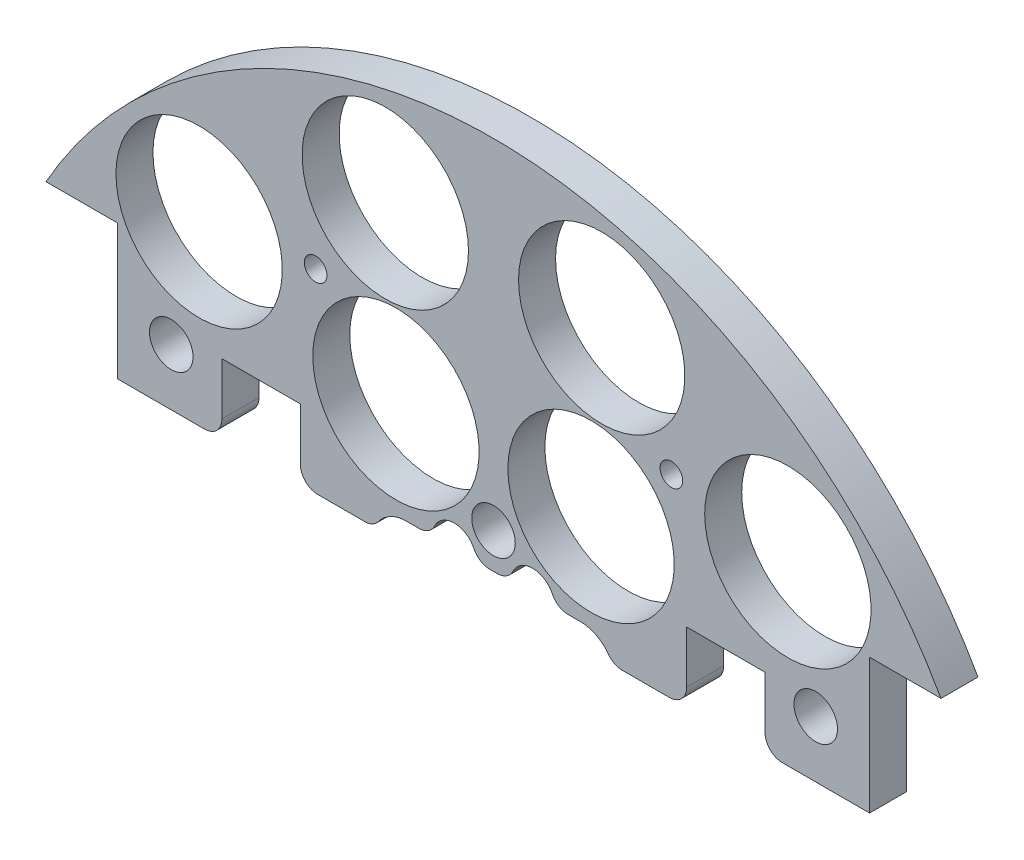
SolidWorks part; units mm, degrees
ref_plane "Front Plane" through (0, 0, 0) normal (0, 0, 1) x (1, 0, 0)
ref_plane "Top Plane" through (0, 0, 0) normal (0, 1, 0) x (1, 0, 0)
ref_plane "Right Plane" through (0, 0, 0) normal (1, 0, 0) x (0, 0, -1)
sketch "Sketch1" plane through (0, 0, 0) normal (0, 0, 1) x (1, 0, 0)
  line L0 (0, 0) -> (-82.1241, 0) construction
  line L1 (0, 0) -> (0, 95.6219) construction
  line L3 (-65.2538, 36.83) -> (-54.8398, 36.83)
  line L5 (-65.2538, -36.83) -> (-54.8398, -36.83)
  line L6 (-54.8398, 36.83) -> (-54.8398, -36.83)
  line L7 (65.2538, -36.83) -> (54.8398, -36.83)
  line L8 (65.2538, 36.83) -> (54.8398, 36.83)
  line L9 (54.8398, 36.83) -> (54.8398, -36.83)
  arc A0 (-65.2538, -36.83) -> (65.2538, -36.83) centre (0, 0) ccw
  circle A1 centre (-45.466, 11.049) radius 1.651
  circle A2 centre (-20.0673, 10.795) radius 1.651
  circle A3 centre (-20.0673, -10.795) radius 1.651
  circle A4 centre (-45.466, -11.049) radius 1.651
  circle A5 centre (45.466, -11.049) radius 1.651
  circle A6 centre (20.0673, -10.795) radius 1.651
  circle A7 centre (20.0673, 10.795) radius 1.651
  circle A8 centre (45.466, 11.049) radius 1.651
  arc A9 (65.2538, 36.83) -> (-65.2538, 36.83) centre (0, 0) ccw
  dimension "D2" = 3.302
  dimension "D3" = 3.302
  dimension "D4" = 25.4
  dimension "D5" = 10.795
  dimension "D10" = 45.466
  dimension "D6" = 73.66
  dimension "D7" = 10.414
  dimension "D8" = 74.93
  dimension "D9" = 74.93
  dimension "D11" = 36.83
extrude "Boss-Extrude2" add sketch "Sketch1" along normal blind 5.3975
sketch "Sketch2" plane through (0, 0, 5.3975) normal (0, 0, 1) x (1, 0, 0)
  line L0 (0, 68.58) -> (0, 55.88) construction
  line L1 (-9.525, 68.58) -> (9.525, 68.58)
  line L2 (-9.525, 68.58) -> (-9.525, 55.88)
  line L3 (-9.525, 55.88) -> (9.525, 55.88)
  line L4 (9.525, 68.58) -> (9.525, 55.88)
  line L5 (-9.525, 62.23) -> (9.525, 62.23) construction
  arc A0 (65.2538, 36.83) -> (-65.2538, 36.83) centre (0, 0) ccw construction
  circle A1 centre (-20.0673, 10.795) radius 1.651 construction
  circle A2 centre (20.0673, 10.795) radius 1.651 construction
  circle A3 centre (-6.731, 62.23) radius 1.143
  circle A4 centre (6.731, 62.23) radius 1.143
  dimension "D4" = 2.286
  dimension "D5" = 0
  dimension "D6" = 6.731
  dimension "D1" = 19.05
  dimension "D2" = 12.7
  dimension "D3" = 55.88
extrude "Cut-Extrude1" cut sketch "Sketch2" against normal through all contours A3 | A4
sketch "Sketch3" plane through (0, 0, 0) normal (0, 0, -1) x (-1, 0, 0)
  line L0 (0, 0) -> (0, -116.2908) construction
  line L1 (0, 0) -> (-153.8039, 0) construction
  circle A0 centre (-14.224, -56.7251) radius 12.1285
  circle A3 centre (14.224, -56.7251) radius 12.1285
  circle A4 centre (-42.926, -42.926) radius 12.1285
  circle A5 centre (14.224, 34.29) radius 12.1285
  circle A6 centre (-14.224, 34.29) radius 12.1285
  circle A8 centre (-42.926, 42.926) radius 12.1285
  circle A11 centre (42.926, 42.926) radius 12.1285
  circle A14 centre (42.926, -42.926) radius 12.1285
  point P36 (0, 0)
  point P53 (0, 0)
  point P55 (0, 0)
  dimension "D1" = 34.29
  dimension "D2" = 14.224
  dimension "D3" = 24.257
  dimension "D4" = 42.926
  dimension "D5" = 42.926
extrude "Cut-Extrude2" cut sketch "Sketch3" against normal through all
sketch "Sketch4" plane through (0, 0, 0) normal (0, 0, -1) x (-1, 0, 0)
  line L1 (-15.7702, 56.3138) -> (12.7925, 56.3138)
  line L2 (-15.7702, 56.3138) -> (-15.7702, 67.9913)
  line L3 (-15.7702, 67.9913) -> (12.7925, 67.9913)
  line L4 (12.7925, 56.3138) -> (12.7925, 67.9913)
extrude "Boss-Extrude3" add sketch "Sketch4" against normal up to surface (5.3975 mm away) up to face at (-55.0545, -42.926, 5.3975)
sketch "Sketch5" plane through (0, 0, 0) normal (0, 0, -1) x (-1, 0, 0)
  line L1 (-113.3786, -90.442) -> (117.3207, -90.442)
  line L2 (-113.3786, -90.442) -> (-113.3786, 17.145)
  line L3 (-113.3786, 17.145) -> (117.3207, 17.145)
  line L4 (117.3207, -90.442) -> (117.3207, 17.145)
  circle A1 centre (20.0673, 10.795) radius 1.651 construction
  dimension "D1" = 6.35
extrude "Cut-Extrude3" cut sketch "Sketch5" against normal through all
sketch "Sketch6" plane through (0, 0, 0) normal (0, 0, -1) x (-1, 0, 0)
  line L0 (0, 0) -> (0, 74.93) construction
  line L1 (0, 0) -> (-15.5068, 57.8721) construction
  arc A0 (65.2538, 36.83) -> (-65.2538, 36.83) centre (0, 0) ccw construction
  circle A1 centre (-15.7776, 58.8828) radius 12.1285
  circle A3 centre (15.7776, 58.8828) radius 12.1285
  dimension "D1" = 24.257
  dimension "D2" = 0
  dimension "D4" = 60.96
  dimension "D3" = 15
extrude "Cut-Extrude4" cut sketch "Sketch6" against normal through all
extrude "Cut-Extrude55" cut sketch "Sketch57" against normal through all both and the other way through all
sketch "Sketch57" plane through (-29.8755, 133.1307, 31.75) normal (0, 0, 1) x (0.01, 0.9999, 0)
  line L0 (-132.559, -31.3134) -> (-132.559, 57.8454) construction
  line L1 (-132.559, -31.3134) -> (-222.516, -31.3134) construction
  circle A0 centre (-157.959, 14.4066) radius 3.175
  circle A1 centre (-173.199, -31.3134) radius 3.175
  circle A3 centre (-157.959, -77.0334) radius 3.175
  circle A4 centre (-107.159, -77.0334) radius 3.175
  circle A5 centre (-91.919, -31.3134) radius 3.175
  circle A6 centre (-107.159, 14.4066) radius 3.175
sketch "Sketch58" [suppressed] plane through (0, 0, 0) normal (0, 0, -1) x (-1, 0, 0)
  circle A0 centre (-46.0825, 25.2068) radius 4.445
  circle A1 centre (-0.5172, 40.9032) radius 4.445
  circle A2 centre (45.3529, 26.1212) radius 4.445
  circle A3 centre (-46.0825, 25.2068) radius 3.175 construction
  circle A4 centre (-0.5172, 40.9032) radius 3.175 construction
  circle A5 centre (45.3529, 26.1212) radius 3.175 construction
  dimension "D1" = 1.27
  dimension "D2" = 1.27
  dimension "D3" = 1.27
extrude "Boss-Extrude4" [suppressed] add sketch "Sketch58" against normal up to surface (6.35 mm away)
extrude "Cut-Extrude56" cut sketch "Sketch59" against normal through all both and the other way through all
sketch "Sketch59" plane through (31.3134, 132.614, -19.05) normal (0, 0, -1) x (0, 1, 0)
  line L0 (-132.614, -31.3134) -> (-132.614, 57.8454) construction
  line L1 (-132.614, -31.3134) -> (-222.516, -31.3134) construction
  circle A0 centre (-158.014, 14.4066) radius 3.175
  circle A1 centre (-173.254, -31.3134) radius 3.175
  circle A3 centre (-158.014, -77.0334) radius 3.175
  circle A4 centre (-107.214, -77.0334) radius 3.175
  circle A5 centre (-91.974, -31.3134) radius 3.175
  circle A6 centre (-107.214, 14.4066) radius 3.175
extrude "Cut-Extrude60" cut sketch "Sketch63" against normal blind 29.21
sketch "Sketch63" plane through (31.3134, 132.614, -15.875) normal (0, 0, -1) x (0, 1, 0)
  line L0 (-132.559, -31.3134) -> (6.1626, -31.3134) construction
  line L2 (-132.559, -31.3134) -> (-132.559, -122.6589) construction
  circle A0 centre (-190.979, 2.9766) radius 1.651
  circle A2 centre (-154.784, -31.3134) radius 1.651
  circle A3 centre (-190.979, -65.6034) radius 1.651
  circle A4 centre (-110.334, -31.3134) radius 1.651
  circle A5 centre (-74.139, -65.6034) radius 1.651
  circle A6 centre (-74.139, 2.9766) radius 1.651
extrude "Cut-Extrude158" cut sketch "Sketch161" against normal blind 29.21
sketch "Sketch161" plane through (-31.3134, 132.559, 6.35) normal (0, 0, 1) x (0, 1, 0)
  line L0 (-143.7712, -34.3645) -> (6.1626, -34.3645) construction
  line L2 (-143.7712, -34.3645) -> (-143.7712, -122.6589) construction
  circle A0 centre (-202.1912, -0.0745) radius 1.651
  circle A2 centre (-165.9962, -34.3645) radius 1.651
  circle A3 centre (-202.1912, -68.6545) radius 1.651
  circle A4 centre (-121.5462, -34.3645) radius 1.651
  circle A5 centre (-85.3512, -68.6545) radius 1.651
  circle A6 centre (-85.3512, -0.0745) radius 1.651
sketch "Sketch162" plane through (0, 0, 5.3975) normal (0, 0, 1) x (1, 0, 0)
  line L0 (-54.8398, 17.145) -> (54.8398, 17.145) construction
  line L1 (39.5998, 17.145) -> (28.1698, 17.145)
  line L2 (39.5998, 17.145) -> (39.5998, 27.305)
  line L3 (39.5998, 27.305) -> (28.1698, 27.305)
  line L4 (28.1698, 17.145) -> (28.1698, 27.305)
  line L5 (0, -4.3124) -> (0, 89.5869) construction
  line L6 (-28.1698, 17.145) -> (-39.5998, 17.145)
  line L7 (-28.1698, 17.145) -> (-28.1698, 27.305)
  line L8 (-28.1698, 27.305) -> (-39.5998, 27.305)
  line L9 (-39.5998, 17.145) -> (-39.5998, 27.305)
  line L10 (54.8398, 17.145) -> (54.8398, 36.83) construction
  dimension "D1" = 10.16
  dimension "D2" = 11.43
  dimension "D3" = 15.24
extrude "Cut-Extrude159" cut sketch "Sketch162" against normal through all
sketch "Sketch202" plane through (0, 0, 0) normal (0, 0, -1) x (-1, 0, 0)
  line L0 (0, 0) -> (0, 91.2173) construction
  circle A0 centre (25.9376, 45.466) radius 1.651
  circle A1 centre (42.926, 42.926) radius 12.1285 construction
  circle A2 centre (15.7776, 58.8828) radius 12.1285 construction
  circle A3 centre (-25.9376, 45.466) radius 1.651
  dimension "D1" = 3.302
  dimension "D3" = 10.16
  dimension "D2" = 2.54
extrude "Cut-Extrude199" cut sketch "Sketch202" against normal blind 35.56
extrude "Cut-Extrude200" cut sketch "Sketch203" against normal blind 48.768 and the other way blind 103.378
sketch "Sketch203" plane through (30.092, 4.0835, 30.734) normal (0, 0, -1) x (-1, 0, 0)
  line L0 (30.092, -4.0835) -> (148.6336, -4.0835) construction
  line L1 (30.092, -4.0835) -> (30.092, 90.452) construction
  circle A0 centre (-16.898, 21.3165) radius 3.175
  circle A1 centre (77.082, 21.3165) radius 3.175
  circle A2 centre (30.092, 21.3165) radius 3.175
  circle A4 centre (77.082, -29.4835) radius 3.175
  circle A5 centre (30.092, -29.4835) radius 3.175
  circle A6 centre (-16.898, -29.4835) radius 3.175
sketch "Sketch165" plane through (0, 0, 0) normal (0, 0, -1) x (-1, 0, 0)
  line L0 (0, 0) -> (0, 12.9674) construction
  line L1 (12.7, 20.24) -> (8.889, 20.24)
  line L2 (7.7, 15.24) -> (-7.7, 15.24)
  line L3 (-8.889, 20.24) -> (-12.7, 20.24)
  line L4 (2.541, 20.24) -> (-2.541, 20.24)
  arc A0 (7.7, 15.24) -> (12.7, 20.24) centre (12.7, 15.24) ccw
  arc A1 (-7.7, 15.24) -> (-12.7, 20.24) centre (-12.7, 15.24) cw
  arc A2 (8.889, 20.24) -> (2.541, 20.24) centre (5.715, 20.32) ccw
  arc A3 (-2.541, 20.24) -> (-8.889, 20.24) centre (-5.715, 20.32) ccw
  dimension "D1" = 10
  dimension "D4" = 6.35
  dimension "D5" = 6.35
  dimension "D2" = 15.24
  dimension "D3" = 12.7
  dimension "D6" = 11.43
  dimension "D7" = 5.715
  dimension "D8" = 20.32
extrude "Cut-Extrude162" cut sketch "Sketch165" against normal blind 30.48
fillet "Fillet1" radius 2.54 10 edges at (39.5998, 17.145, 2.6987) (28.1698, 17.145, 2.6987) (17.3229, 17.145, 2.6987) (8.889, 20.24, 2.6987) (2.541, 20.24, 2.6987) (-2.541, 20.24, 2.6987) (-8.889, 20.24, 2.6987) (-17.3229, 17.145, 2.6987) (-28.1698, 17.145, 2.6987) (-39.5998, 17.145, 2.6987)
